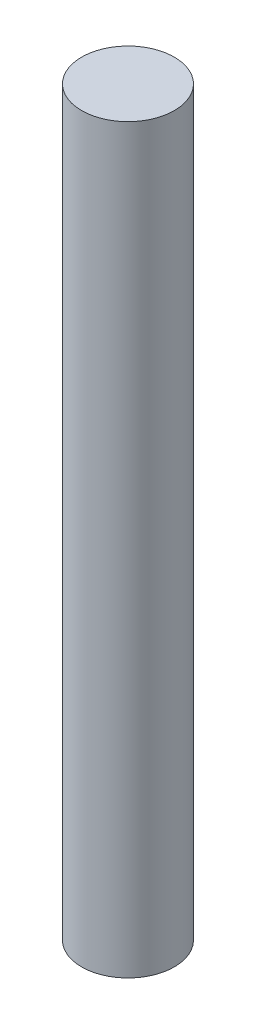
SolidWorks part; units mm, degrees
ref_plane "Front Plane" through (0, 0, 0) normal (0, 0, 1) x (1, 0, 0)
ref_plane "Top Plane" through (0, 0, 0) normal (0, 1, 0) x (1, 0, 0)
ref_plane "Right Plane" through (0, 0, 0) normal (1, 0, 0) x (0, 0, -1)
sketch "Sketch1" plane through (0, 0, 0) normal (0, 1, 0) x (1, 0, 0)
  circle A0 centre (0, 0) radius 2.5
  dimension "D1" = 5
extrude "Boss-Extrude1" add sketch "Sketch1" along normal blind 40
